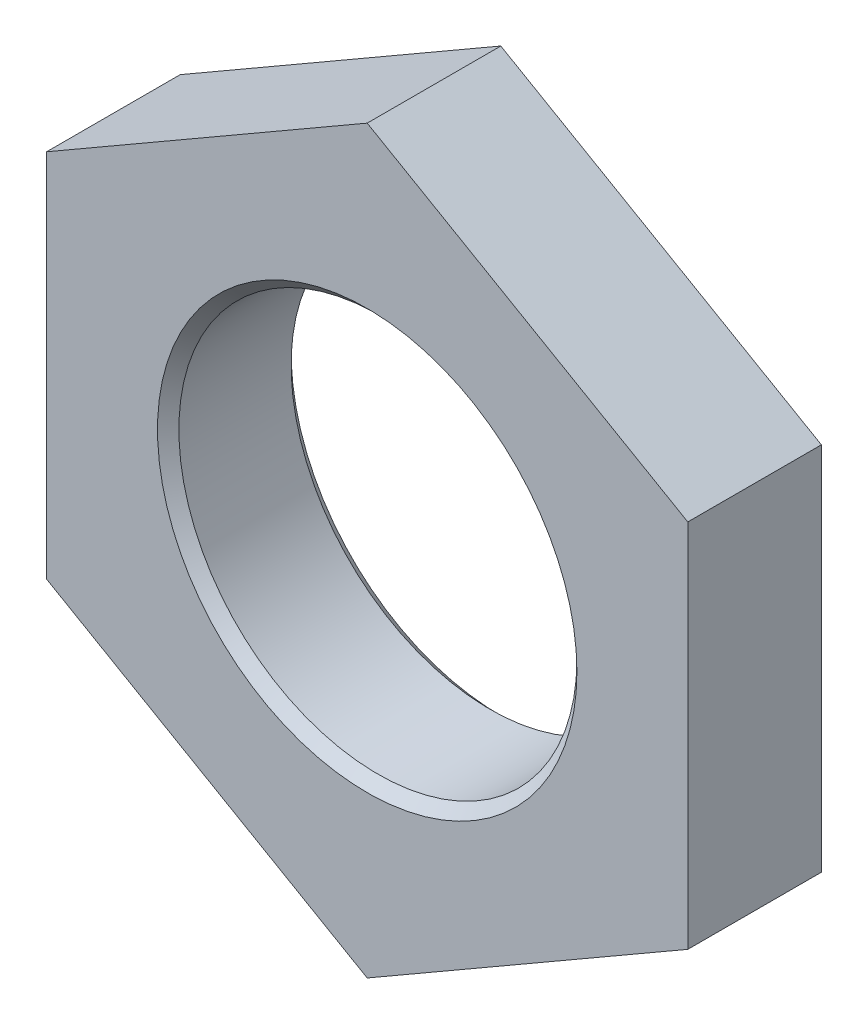
SolidWorks part; units mm, degrees
ref_plane "前视基准面" through (0, 0, 0) normal (0, 0, 1) x (1, 0, 0)
ref_plane "上视基准面" through (0, 0, 0) normal (0, 1, 0) x (1, 0, 0)
ref_plane "右视基准面" through (0, 0, 0) normal (1, 0, 0) x (0, 0, -1)
sketch "草图2" plane through (0, 0, 0) normal (0, 0, 1) x (1, 0, 0)
  line L1 (0, 6.9282) -> (-6, 3.4641)
  line L2 (-6, 3.4641) -> (-6, -3.4641)
  line L3 (-6, -3.4641) -> (0, -6.9282)
  line L4 (0, -6.9282) -> (6, -3.4641)
  line L5 (6, -3.4641) -> (6, 3.4641)
  line L6 (6, 3.4641) -> (0, 6.9282)
  circle A0 centre (0, 0) radius 6 construction
  point P1 (0, 0)
  point P10 (0, 0)
  point P11 (0, 0)
  point P12 (0, 0)
  point P13 (0, 0)
  point P14 (0, 0)
  point P15 (0, 0)
  point P16 (0, 0)
  point P17 (0, 0)
  point P18 (6, 0)
  dimension "D1" = 12
extrude "凸台-拉伸1" add sketch "草图2" along normal blind 2.5
sketch "草图3" plane through (0, 0, 0) normal (0, 0, -1) x (-1, 0, 0)
  circle A0 centre (0, 0) radius 3.725
extrude "切除-拉伸1" cut sketch "草图3" against normal blind 6.5
cosmetic thread "装饰螺纹线1" parameters "D1"=2.5, "D2"=10
chamfer "倒角1" distance 0.2 angle 45 2 edges at (3.725, 0, 2.5) (-3.725, 0, 0)
